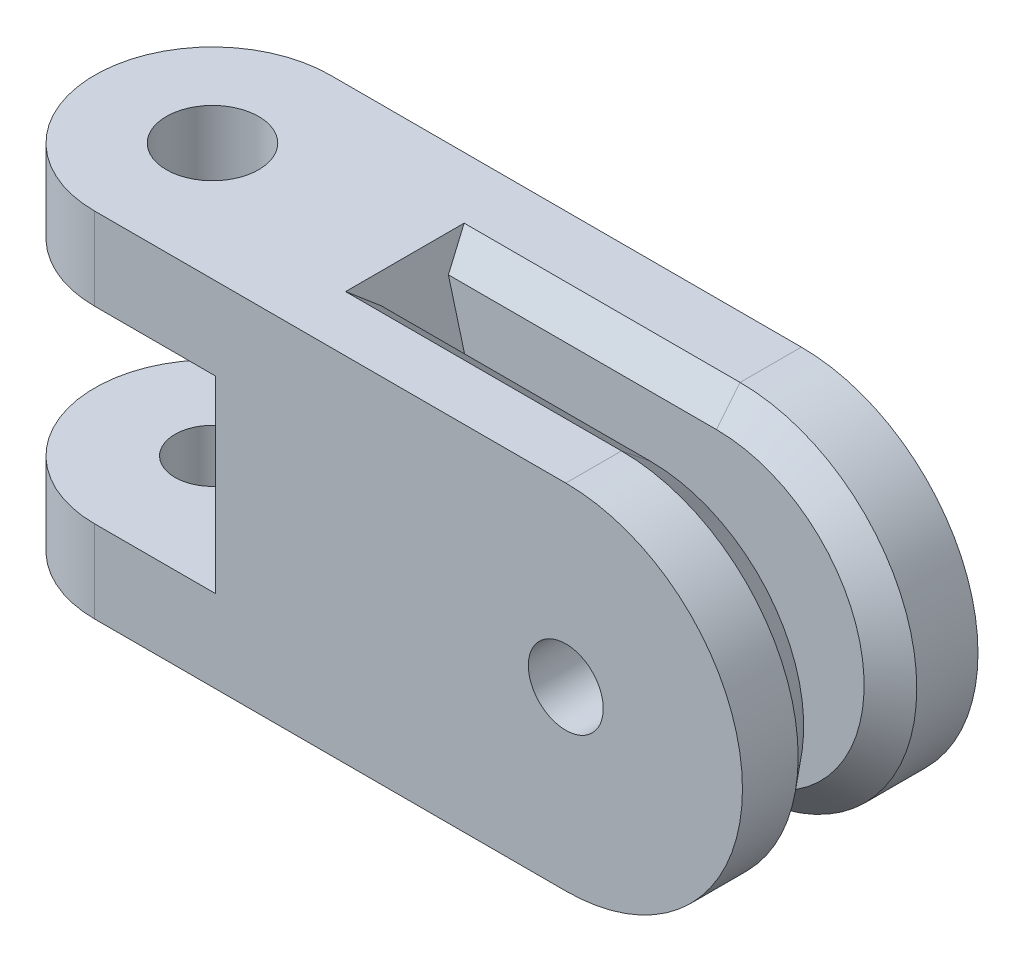
SolidWorks part; units mm, degrees
ref_plane "Front Plane" through (0, 0, 0) normal (0, 0, 1) x (1, 0, 0)
ref_plane "Top Plane" through (0, 0, 0) normal (0, 1, 0) x (1, 0, 0)
ref_plane "Right Plane" through (0, 0, 0) normal (1, 0, 0) x (0, 0, -1)
sketch "Sketch1" plane through (0, 0, 0) normal (0, 1, 0) x (1, 0, 0)
  line L0 (0, 0) -> (-19.05, 0) construction
  line L1 (0, -6.35) -> (-19.05, -6.35)
  line L2 (0, 6.35) -> (-19.05, 6.35)
  line L3 (0, 6.35) -> (0, -6.35)
  arc A1 (-19.05, 6.35) -> (-19.05, -6.35) centre (-19.05, 0) ccw
  point P3 (-9.525, 0)
  point P8 (-16.925, 6.2626)
  dimension "D2" = 6.35
  dimension "D1" = 19.05
extrude "Boss-Extrude1" add sketch "Sketch1" along normal mid plane 19.05
sketch "Sketch2" plane through (0, 0, 6.35) normal (0, 0, 1) x (1, 0, 0)
  line L0 (0, 0) -> (6.35, 0) construction
  line L1 (0, 9.525) -> (0, -9.525) construction
  line L2 (0, 9.525) -> (6.35, 9.525)
  line L3 (0, -9.525) -> (6.35, -9.525)
  line L4 (-19.05, 9.525) -> (0, 9.525) construction
  arc A0 (0, 9.525) -> (0, -9.525) centre (0, 0) ccw
  arc A1 (6.35, -9.525) -> (6.35, 9.525) centre (6.35, 0) ccw
  point P4 (3.175, 0)
  dimension "D1" = 6.35
extrude "Boss-Extrude2" add sketch "Sketch2" against normal up to surface (12.7 mm away) up to face at (-9.525, 0, -6.35)
sketch "Sketch3" plane through (0, 0, 0) normal (0, 1, 0) x (1, 0, 0)
  line L0 (6.35, 6.35) -> (-19.05, 6.35) construction
  line L1 (-19.05, -6.35) -> (6.35, -6.35) construction
  line L2 (-12.5265, 6.35) -> (-19.05, 6.35)
  line L3 (-19.05, -6.35) -> (-12.5265, -6.35)
  line L4 (-12.5265, -6.35) -> (-12.5265, 6.35)
  arc A0 (-19.05, 6.35) -> (-19.05, -6.35) centre (-19.05, 0) ccw construction
  arc A1 (-19.05, 6.35) -> (-19.05, -6.35) centre (-19.05, 0) ccw
  dimension "D1" = 6.5235
extrude "Cut-Extrude1" cut sketch "Sketch3" against normal mid plane 10.16
hole_wizard "#10-32 Tapped Hole1" positions "Sketch4" profile "Sketch5" tap size "#10-32" standard "ANSI Inch"
sketch "Sketch4" plane through (0, -5.08, 0) normal (0, 1, 0) x (1, 0, 0)
  point P0 (-19.05, 0)
sketch "Sketch5" plane through (-19.05, -5.08, 0) normal (1, 0, 0) x (0, 0, 1)
  line L0 (0, 0) -> (0, 4.445)
  line L1 (0, 4.445) -> (2.0193, 4.445)
  line L2 (2.0193, 4.445) -> (2.0193, 0)
  line L5 (2.0193, 0) -> (0, 0)
  line L11 (0, -6.35) -> (0, 107.95) construction
  dimension "Thru Tap Drill Dia." = 4.0386
  dimension "Thru Tap Drill Depth" = 4.445
cosmetic thread "Hole Thread1" parameters "D2"=4.826
hole_wizard "#10 Clearance Hole1" positions "Sketch6" profile "Sketch8" hole size "#10" standard "ANSI Inch"
sketch "Sketch6" plane through (0, 9.525, 0) normal (0, 1, 0) x (1, 0, 0)
  point P0 (-19.05, 0)
sketch "Sketch8" plane through (-19.05, 9.525, 0) normal (1, 0, 0) x (0, 0, 1)
  line L0 (0, 0) -> (0, 16.0997)
  line L1 (0, 16.0997) -> (2.4892, 14.604)
  line L2 (2.4892, 14.604) -> (2.4892, 0)
  line L5 (2.4892, 0) -> (0, 0)
  line L10 (0, 16.0997) -> (-2.4892, 14.604) construction
  line L11 (0, -6.35) -> (0, 107.95) construction
  dimension "Hole Dia." = 4.9784
  dimension "Hole Depth" = 14.604
  dimension "Drill Angle" = 118
sketch "Sketch9" plane through (0, 0, 0) normal (0, 0, 1) x (1, 0, 0)
  line L0 (-5.9763, 0) -> (-8.5285, -9.525)
  line L1 (-8.5285, -9.525) -> (6.35, -9.525)
  line L3 (6.35, 9.525) -> (-8.5285, 9.525)
  line L4 (-8.5285, 9.525) -> (-5.9763, 0)
  line L5 (6.35, -9.525) -> (-19.05, -9.525) construction
  arc A0 (6.35, -9.525) -> (6.35, 9.525) centre (6.35, 0) ccw
  arc A1 (6.35, -9.525) -> (6.35, 9.525) centre (6.35, 0) ccw construction
  circle A2 centre (6.35, 0) radius 11.9062 construction
  dimension "D2" = 23.8125
  dimension "D1" = 150
extrude "Cut-Extrude2" cut sketch "Sketch9" along normal mid plane 3.556
hole_wizard "#10 Clearance Hole2" positions "Sketch10" profile "Sketch11" hole size "#10" standard "ANSI Inch"
sketch "Sketch10" plane through (0, 0, -6.35) normal (0, 0, -1) x (-1, 0, 0)
  point P0 (-6.35, 0)
sketch "Sketch11" plane through (6.35, 0, -6.35) normal (1, 0, 0) x (0, 1, 0)
  line L0 (0, 0) -> (0, 9.6227)
  line L1 (0, 9.6227) -> (2.4892, 8.127)
  line L2 (2.4892, 8.127) -> (2.4892, 0)
  line L5 (2.4892, 0) -> (0, 0)
  line L10 (0, 9.6227) -> (-2.4892, 8.127) construction
  line L11 (0, -6.35) -> (0, 107.95) construction
  dimension "Hole Dia." = 4.9784
  dimension "Hole Depth" = 8.127
  dimension "Drill Angle" = 118
hole_wizard "#10-32 Tapped Hole2" positions "Sketch12" profile "Sketch13" tap size "#10-32" standard "ANSI Inch" end condition through all
sketch "Sketch12" plane through (0, 0, 1.778) normal (0, 0, -1) x (-1, 0, 0)
  point P0 (-6.35, 0)
sketch "Sketch13" plane through (6.35, 0, 1.778) normal (1, 0, 0) x (0, 1, 0)
  line L0 (0, 0) -> (0, 4.572)
  line L1 (0, 4.572) -> (2.0193, 4.572)
  line L2 (2.0193, 4.572) -> (2.0193, 0)
  line L5 (2.0193, 0) -> (0, 0)
  line L11 (0, -6.35) -> (0, 107.95) construction
  dimension "Thru Tap Drill Dia." = 4.0386
  dimension "Thru Tap Drill Depth" = 4.572
cosmetic thread "Hole Thread2" parameters "D2"=4.826
chamfer "Chamfer1" distance 1.27 angle 51 6 edges at (-1.0892, -9.525, 1.778) (-1.0892, 9.525, 1.778) (15.875, 0, 1.778) (-1.0892, -9.525, -1.778) (-1.0892, 9.525, -1.778) (15.875, 0, -1.778)
equation "\"D1@Sketch3\"=.1875+1.38mm+.015"
